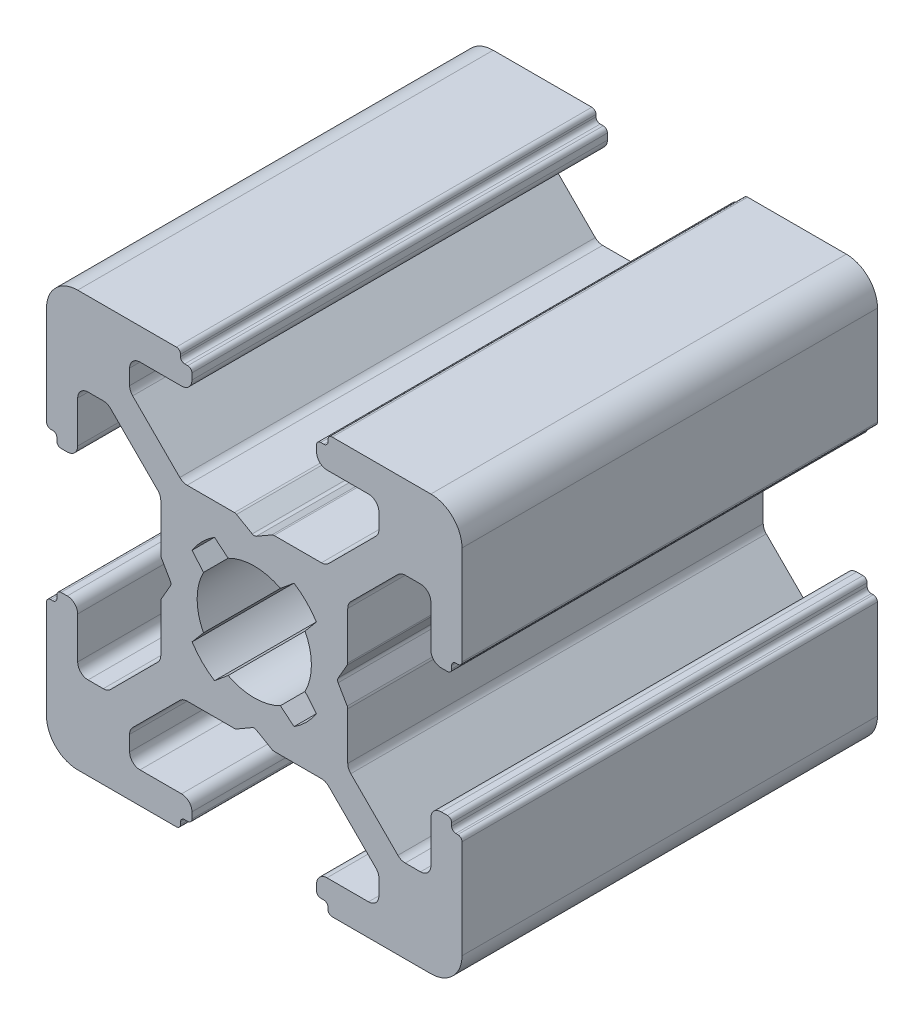
SolidWorks part; units mm, degrees
ref_plane "Płaszczyzna przednia" through (0, 0, 0) normal (0, 0, 1) x (1, 0, 0)
ref_plane "Płaszczyzna górna" through (0, 0, 0) normal (0, 1, 0) x (1, 0, 0)
ref_plane "Płaszczyzna prawa" through (0, 0, 0) normal (1, 0, 0) x (0, 0, -1)
sketch "Szkic1" plane through (0, 0, 0) normal (0, 0, 1) x (1, 0, 0)
  line L0 (7.0078, -1.8401) -> (7.5547, -2.4918)
  line L1 (7.5547, -5.0082) -> (7.0078, -5.6599)
  line L2 (8.0861, -6.7396) -> (8.7418, -6.1953)
  line L3 (11.2582, -6.1953) -> (11.9139, -6.7396)
  line L4 (12.9922, -5.6599) -> (12.4453, -5.0082)
  line L5 (12.4453, -2.4918) -> (12.9922, -1.8401)
  line L6 (11.9139, -0.7604) -> (11.2582, -1.3047)
  line L7 (8.7418, -1.3047) -> (8.0861, -0.7604)
  line L8 (6.25, 6.25) -> (1.5, 6.25)
  line L9 (6.45, 5.95) -> (6.45, 6.05)
  line L10 (6.8, 5.75) -> (6.65, 5.75)
  line L11 (7, 5.25) -> (7, 5.55)
  line L12 (4.5, 4.75) -> (6.5, 4.75)
  line L13 (4, 3.5178) -> (4, 4.25)
  line L14 (6.4142, 0.8964) -> (4.1464, 3.1642)
  line L15 (9.0464, 0.75) -> (6.7678, 0.75)
  line L16 (9.9, 0.2881) -> (9.1464, 0.7232)
  line L17 (10.8536, 0.7232) -> (10.1, 0.2881)
  line L18 (13.2322, 0.75) -> (10.9536, 0.75)
  line L19 (15.8536, 3.1642) -> (13.5858, 0.8964)
  line L20 (16, 4.25) -> (16, 3.5178)
  line L21 (13.5, 4.75) -> (15.5, 4.75)
  line L22 (13, 5.55) -> (13, 5.25)
  line L23 (13.35, 5.75) -> (13.2, 5.75)
  line L24 (13.55, 6.05) -> (13.55, 5.95)
  line L25 (18.5, 6.25) -> (13.75, 6.25)
  line L26 (20, 0) -> (20, 4.75)
  line L27 (19.7, -0.2) -> (19.8, -0.2)
  line L28 (19.5, -0.55) -> (19.5, -0.4)
  line L29 (19, -0.75) -> (19.3, -0.75)
  line L30 (18.5, 1.75) -> (18.5, -0.25)
  line L31 (17.2678, 2.25) -> (18, 2.25)
  line L32 (14.6464, -0.1642) -> (16.9142, 2.1036)
  line L33 (14.5, -2.7964) -> (14.5, -0.5178)
  line L34 (14.0381, -3.65) -> (14.4732, -2.8964)
  line L35 (14.4732, -4.6036) -> (14.0381, -3.85)
  line L36 (14.5, -6.9822) -> (14.5, -4.7036)
  line L37 (16.9142, -9.6036) -> (14.6464, -7.3358)
  line L38 (18, -9.75) -> (17.2678, -9.75)
  line L39 (18.5, -7.25) -> (18.5, -9.25)
  line L40 (19.3, -6.75) -> (19, -6.75)
  line L41 (19.5, -7.1) -> (19.5, -6.95)
  line L42 (19.8, -7.3) -> (19.7, -7.3)
  line L43 (20, -12.25) -> (20, -7.5)
  line L44 (13.75, -13.75) -> (18.5, -13.75)
  line L45 (13.55, -13.45) -> (13.55, -13.55)
  line L46 (13.2, -13.25) -> (13.35, -13.25)
  line L47 (13, -12.75) -> (13, -13.05)
  line L48 (15.5, -12.25) -> (13.5, -12.25)
  line L49 (16, -11.0178) -> (16, -11.75)
  line L50 (13.5858, -8.3964) -> (15.8536, -10.6642)
  line L51 (10.9536, -8.25) -> (13.2322, -8.25)
  line L52 (10.1, -7.7881) -> (10.8536, -8.2232)
  line L53 (9.1464, -8.2232) -> (9.9, -7.7881)
  line L54 (6.7678, -8.25) -> (9.0464, -8.25)
  line L55 (4.1464, -10.6642) -> (6.4142, -8.3964)
  line L56 (4, -11.75) -> (4, -11.0178)
  line L57 (6.5, -12.25) -> (4.5, -12.25)
  line L58 (7, -13.05) -> (7, -12.75)
  line L59 (6.65, -13.25) -> (6.8, -13.25)
  line L60 (6.45, -13.55) -> (6.45, -13.45)
  line L61 (1.5, -13.75) -> (6.25, -13.75)
  line L62 (0, -7.5) -> (0, -12.25)
  line L63 (0.3, -7.3) -> (0.2, -7.3)
  line L64 (0.5, -6.95) -> (0.5, -7.1)
  line L65 (1, -6.75) -> (0.7, -6.75)
  line L66 (1.5, -9.25) -> (1.5, -7.25)
  line L67 (2.7322, -9.75) -> (2, -9.75)
  line L68 (5.3536, -7.3358) -> (3.0858, -9.6036)
  line L69 (5.5, -4.7036) -> (5.5, -6.9822)
  line L70 (5.9619, -3.85) -> (5.5268, -4.6036)
  line L71 (5.5268, -2.8964) -> (5.9619, -3.65)
  line L72 (5.5, -0.5178) -> (5.5, -2.7964)
  line L73 (3.0858, 2.1036) -> (5.3536, -0.1642)
  line L74 (2, 2.25) -> (2.7322, 2.25)
  line L75 (1.5, -0.25) -> (1.5, 1.75)
  line L76 (0.7, -0.75) -> (1, -0.75)
  line L77 (0.5, -0.4) -> (0.5, -0.55)
  line L78 (0.2, -0.2) -> (0.3, -0.2)
  line L79 (0, 4.75) -> (0, 0)
  arc A0 (7.5547, -2.4918) -> (7.5547, -5.0082) centre (10, -3.75) ccw
  arc A1 (7.0078, -5.6599) -> (8.0861, -6.7396) centre (10, -3.75) ccw
  arc A2 (8.7418, -6.1953) -> (11.2582, -6.1953) centre (10, -3.75) ccw
  arc A3 (11.9139, -6.7396) -> (12.9922, -5.6599) centre (10, -3.75) ccw
  arc A4 (12.4453, -5.0082) -> (12.4453, -2.4918) centre (10, -3.75) ccw
  arc A5 (12.9922, -1.8401) -> (11.9139, -0.7604) centre (10, -3.75) ccw
  arc A6 (11.2582, -1.3047) -> (8.7418, -1.3047) centre (10, -3.75) ccw
  arc A7 (8.0861, -0.7604) -> (7.0078, -1.8401) centre (10, -3.75) ccw
  arc A8 (6.45, 6.05) -> (6.25, 6.25) centre (6.25, 6.05) ccw
  arc A9 (6.45, 5.95) -> (6.65, 5.75) centre (6.65, 5.95) ccw
  arc A10 (7, 5.55) -> (6.8, 5.75) centre (6.8, 5.55) ccw
  arc A11 (6.5, 4.75) -> (7, 5.25) centre (6.5, 5.25) ccw
  arc A12 (4.5, 4.75) -> (4, 4.25) centre (4.5, 4.25) ccw
  arc A13 (4, 3.5178) -> (4.1464, 3.1642) centre (4.5, 3.5178) ccw
  arc A14 (6.4142, 0.8964) -> (6.7678, 0.75) centre (6.7678, 1.25) ccw
  arc A15 (9.1464, 0.7232) -> (9.0464, 0.75) centre (9.0464, 0.55) ccw
  arc A16 (9.9, 0.2881) -> (10.1, 0.2881) centre (10, 0.4613) ccw
  arc A17 (10.9536, 0.75) -> (10.8536, 0.7232) centre (10.9536, 0.55) ccw
  arc A18 (13.2322, 0.75) -> (13.5858, 0.8964) centre (13.2322, 1.25) ccw
  arc A19 (15.8536, 3.1642) -> (16, 3.5178) centre (15.5, 3.5178) ccw
  arc A20 (16, 4.25) -> (15.5, 4.75) centre (15.5, 4.25) ccw
  arc A21 (13, 5.25) -> (13.5, 4.75) centre (13.5, 5.25) ccw
  arc A22 (13.2, 5.75) -> (13, 5.55) centre (13.2, 5.55) ccw
  arc A23 (13.35, 5.75) -> (13.55, 5.95) centre (13.35, 5.95) ccw
  arc A24 (13.75, 6.25) -> (13.55, 6.05) centre (13.75, 6.05) ccw
  arc A25 (20, 4.75) -> (18.5, 6.25) centre (18.5, 4.75) ccw
  arc A26 (19.8, -0.2) -> (20, 0) centre (19.8, 0) ccw
  arc A27 (19.7, -0.2) -> (19.5, -0.4) centre (19.7, -0.4) ccw
  arc A28 (19.3, -0.75) -> (19.5, -0.55) centre (19.3, -0.55) ccw
  arc A29 (18.5, -0.25) -> (19, -0.75) centre (19, -0.25) ccw
  arc A30 (18.5, 1.75) -> (18, 2.25) centre (18, 1.75) ccw
  arc A31 (17.2678, 2.25) -> (16.9142, 2.1036) centre (17.2678, 1.75) ccw
  arc A32 (14.6464, -0.1642) -> (14.5, -0.5178) centre (15, -0.5178) ccw
  arc A33 (14.4732, -2.8964) -> (14.5, -2.7964) centre (14.3, -2.7964) ccw
  arc A34 (14.0381, -3.65) -> (14.0381, -3.85) centre (14.2113, -3.75) ccw
  arc A35 (14.5, -4.7036) -> (14.4732, -4.6036) centre (14.3, -4.7036) ccw
  arc A36 (14.5, -6.9822) -> (14.6464, -7.3358) centre (15, -6.9822) ccw
  arc A37 (16.9142, -9.6036) -> (17.2678, -9.75) centre (17.2678, -9.25) ccw
  arc A38 (18, -9.75) -> (18.5, -9.25) centre (18, -9.25) ccw
  arc A39 (19, -6.75) -> (18.5, -7.25) centre (19, -7.25) ccw
  arc A40 (19.5, -6.95) -> (19.3, -6.75) centre (19.3, -6.95) ccw
  arc A41 (19.5, -7.1) -> (19.7, -7.3) centre (19.7, -7.1) ccw
  arc A42 (20, -7.5) -> (19.8, -7.3) centre (19.8, -7.5) ccw
  arc A43 (18.5, -13.75) -> (20, -12.25) centre (18.5, -12.25) ccw
  arc A44 (13.55, -13.55) -> (13.75, -13.75) centre (13.75, -13.55) ccw
  arc A45 (13.55, -13.45) -> (13.35, -13.25) centre (13.35, -13.45) ccw
  arc A46 (13, -13.05) -> (13.2, -13.25) centre (13.2, -13.05) ccw
  arc A47 (13.5, -12.25) -> (13, -12.75) centre (13.5, -12.75) ccw
  arc A48 (15.5, -12.25) -> (16, -11.75) centre (15.5, -11.75) ccw
  arc A49 (16, -11.0178) -> (15.8536, -10.6642) centre (15.5, -11.0178) ccw
  arc A50 (13.5858, -8.3964) -> (13.2322, -8.25) centre (13.2322, -8.75) ccw
  arc A51 (10.8536, -8.2232) -> (10.9536, -8.25) centre (10.9536, -8.05) ccw
  arc A52 (10.1, -7.7881) -> (9.9, -7.7881) centre (10, -7.9613) ccw
  arc A53 (9.0464, -8.25) -> (9.1464, -8.2232) centre (9.0464, -8.05) ccw
  arc A54 (6.7678, -8.25) -> (6.4142, -8.3964) centre (6.7678, -8.75) ccw
  arc A55 (4.1464, -10.6642) -> (4, -11.0178) centre (4.5, -11.0178) ccw
  arc A56 (4, -11.75) -> (4.5, -12.25) centre (4.5, -11.75) ccw
  arc A57 (7, -12.75) -> (6.5, -12.25) centre (6.5, -12.75) ccw
  arc A58 (6.8, -13.25) -> (7, -13.05) centre (6.8, -13.05) ccw
  arc A59 (6.65, -13.25) -> (6.45, -13.45) centre (6.65, -13.45) ccw
  arc A60 (6.25, -13.75) -> (6.45, -13.55) centre (6.25, -13.55) ccw
  arc A61 (0, -12.25) -> (1.5, -13.75) centre (1.5, -12.25) ccw
  arc A62 (0.2, -7.3) -> (0, -7.5) centre (0.2, -7.5) ccw
  arc A63 (0.3, -7.3) -> (0.5, -7.1) centre (0.3, -7.1) ccw
  arc A64 (0.7, -6.75) -> (0.5, -6.95) centre (0.7, -6.95) ccw
  arc A65 (1.5, -7.25) -> (1, -6.75) centre (1, -7.25) ccw
  arc A66 (1.5, -9.25) -> (2, -9.75) centre (2, -9.25) ccw
  arc A67 (2.7322, -9.75) -> (3.0858, -9.6036) centre (2.7322, -9.25) ccw
  arc A68 (5.3536, -7.3358) -> (5.5, -6.9822) centre (5, -6.9822) ccw
  arc A69 (5.5268, -4.6036) -> (5.5, -4.7036) centre (5.7, -4.7036) ccw
  arc A70 (5.9619, -3.85) -> (5.9619, -3.65) centre (5.7887, -3.75) ccw
  arc A71 (5.5, -2.7964) -> (5.5268, -2.8964) centre (5.7, -2.7964) ccw
  arc A72 (5.5, -0.5178) -> (5.3536, -0.1642) centre (5, -0.5178) ccw
  arc A73 (3.0858, 2.1036) -> (2.7322, 2.25) centre (2.7322, 1.75) ccw
  arc A74 (2, 2.25) -> (1.5, 1.75) centre (2, 1.75) ccw
  arc A75 (1, -0.75) -> (1.5, -0.25) centre (1, -0.25) ccw
  arc A76 (0.5, -0.55) -> (0.7, -0.75) centre (0.7, -0.55) ccw
  arc A77 (0.5, -0.4) -> (0.3, -0.2) centre (0.3, -0.4) ccw
  arc A78 (0, 0) -> (0.2, -0.2) centre (0.2, 0) ccw
  arc A79 (1.5, 6.25) -> (0, 4.75) centre (1.5, 4.75) ccw
  dimension "D4" = 2.75
  dimension "D1" = 20
  dimension "D2" = 20
  dimension "D3" = 6
extrude "Dodanie-wyciągnięcie1" add sketch "Szkic1" along normal blind 20
